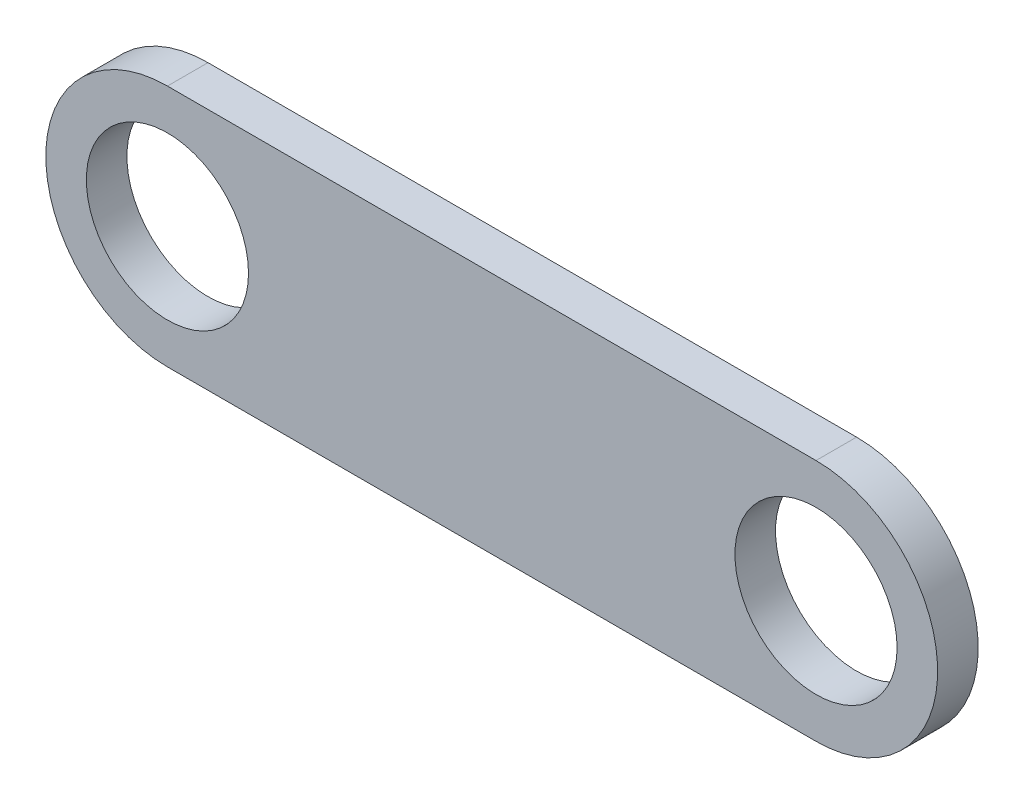
SolidWorks part; units mm, degrees
ref_plane "Alzado" through (0, 0, 0) normal (0, 0, 1) x (1, 0, 0)
ref_plane "Planta" through (0, 0, 0) normal (0, 1, 0) x (1, 0, 0)
ref_plane "Vista lateral" through (0, 0, 0) normal (1, 0, 0) x (0, 0, -1)
sketch "Croquis1" plane through (0, 0, 0) normal (0, 0, 1) x (1, 0, 0)
  line L1 (-28.7629, 11.134) -> (51.2371, 11.134)
  line L3 (-28.7629, -18.866) -> (51.2371, -18.866)
  arc A0 (-28.7629, 11.134) -> (-28.7629, -18.866) centre (-28.7629, -3.866) ccw
  arc A1 (51.2371, -18.866) -> (51.2371, 11.134) centre (51.2371, -3.866) ccw
  circle A2 centre (-28.7629, -3.866) radius 10
  circle A3 centre (51.2371, -3.866) radius 10
  dimension "D3" = 20
  dimension "D4" = 20
  dimension "D1" = 30
  dimension "D2" = 80
extrude "Saliente-Extruir1" add sketch "Croquis1" along normal blind 5
